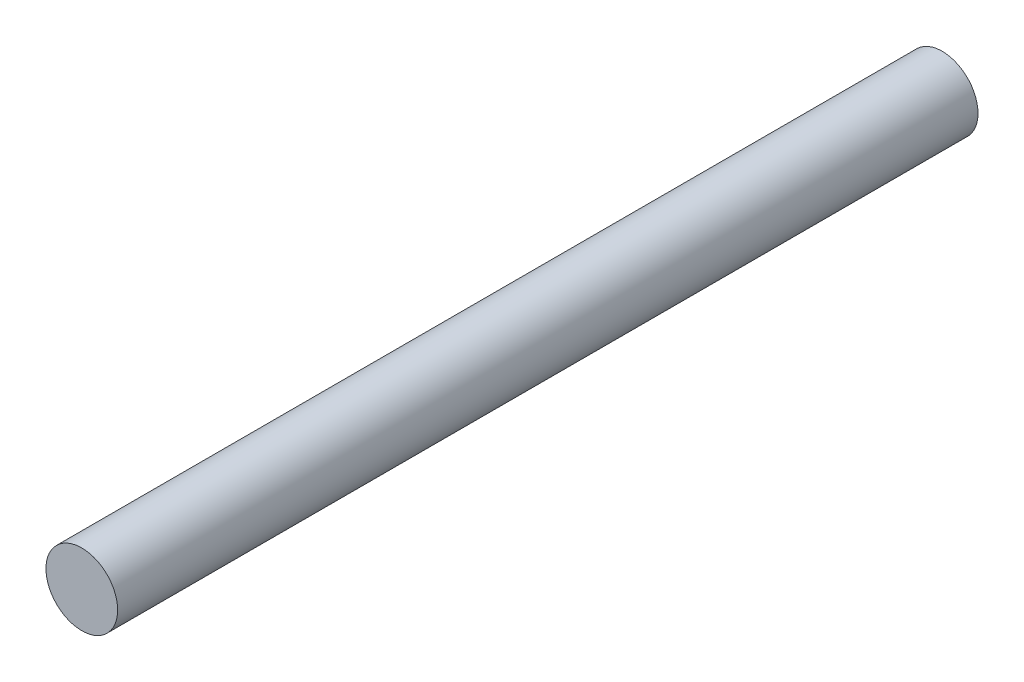
SolidWorks part; units mm, degrees
ref_plane "Front" through (0, 0, 0) normal (0, 0, 1) x (1, 0, 0)
ref_plane "Top" through (0, 0, 0) normal (0, 1, 0) x (1, 0, 0)
ref_plane "Right" through (0, 0, 0) normal (1, 0, 0) x (0, 0, -1)
sketch "Sketch1" plane through (0, 0, 0) normal (0, 0, 1) x (1, 0, 0)
  circle A0 centre (0, 0) radius 2.5
extrude "Boss-Extrude1" add sketch "Sketch1" along normal blind 60
sketch "For Drawing" plane through (0, 0, 0) normal (0, 0, 1) x (1, 0, 0)
  circle A0 centre (0, 0) radius 2.5
  circle A1 centre (0, 0) radius 2.5 construction
  dimension "Diameter" = 5
sketch "Break Point" plane through (0, 0, 0) normal (1, 0, 0) x (0, 0, -1)
  line L0 (-60, 0) -> (-52.5, 0)
  line L1 (-60, 2.5) -> (-60, -2.5) construction
  line L2 (0, 0) -> (-7.5, 0)
  line L3 (-7.5, -2.5) -> (-7.5, 2.5) construction
  line L4 (0, 2.5) -> (-60, 2.5) construction
  line L5 (-52.5, -2.5) -> (-52.5, 2.5) construction
  point P12 (-7.5, 0)
  point P15 (-52.5, 0)
  dimension "D1" = 7.5
equation "\"D1@Break Point\"=\"Diameter@Sketch1\" * 1.5"
